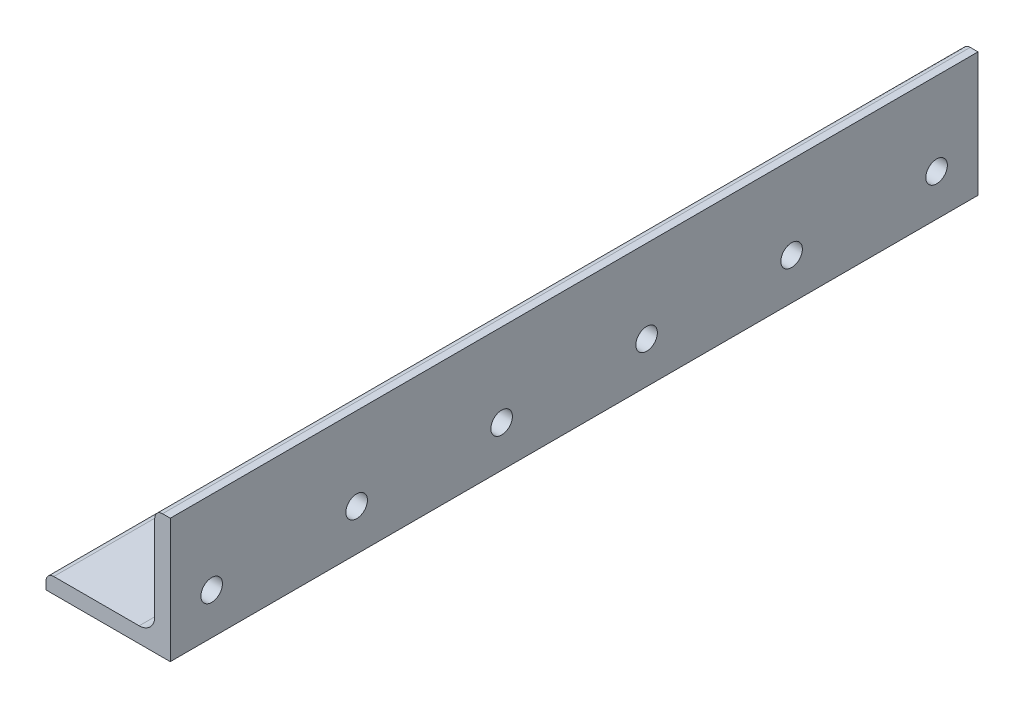
SolidWorks part; units mm, degrees
ref_plane "Front Plane" through (0, 0, 0) normal (0, 0, 1) x (1, 0, 0)
ref_plane "Top Plane" through (0, 0, 0) normal (0, 1, 0) x (1, 0, 0)
ref_plane "Right Plane" through (0, 0, 0) normal (1, 0, 0) x (0, 0, -1)
sketch "Sketch0" plane through (0, 0, 0) normal (0, 0, 1) x (1, 0, 0)
  line L0 (-19.05, -19.05) -> (19.05, -19.05)
  line L1 (19.05, -19.05) -> (19.05, 19.05)
  line L2 (19.05, 0) -> (0, 0) construction
  line L3 (0, 0) -> (0, -19.05) construction
  line L4 (14.2875, -9.5123) -> (14.2875, 19.05) construction
  line L5 (9.5123, -14.2875) -> (-19.05, -14.2875) construction
  arc A0 (14.2875, -9.5123) -> (9.5123, -14.2875) centre (9.5123, -9.5123) cw
  point P3 (12.8889, -12.8889)
  dimension "Inside Corner Radius" = 4.7752
  dimension "Outside Width" = 38.1
  dimension "Wall Thickness" = 4.7625
  dimension "D2" = 4.7625
  dimension "Outside Height" = 38.1
  dimension "Inside Height" = 33.3375
  dimension "Inside Width" = 33.3375
sketch "Sketch1" plane through (0, 0, 0) normal (1, 0, 0) x (0, 0, -1)
  line L0 (152.4, 0) -> (-152.4, 0)
  point P4 (0, 0)
  dimension "Length" = 304.8
sketch "Sketch2" plane through (0, 0, 0) normal (0, 0, 1) x (1, 0, 0)
  line L0 (-19.05, -19.05) -> (19.05, -19.05)
  line L1 (19.05, -19.05) -> (19.05, 19.05)
  line L2 (19.05, 19.05) -> (14.2875, 19.05) construction
  line L3 (14.2875, 16.6688) -> (14.2875, -9.5123)
  line L4 (9.5123, -14.2875) -> (-16.6687, -14.2875)
  line L5 (-19.05, -19.05) -> (-19.05, -14.2875) construction
  line L6 (16.6688, 19.05) -> (19.05, 19.05)
  line L7 (-19.05, -16.6688) -> (-19.05, -19.05)
  line L8 (19.05, 0) -> (0, 0) construction
  line L9 (0, 0) -> (0, -19.05) construction
  arc A0 (14.2875, 16.6688) -> (16.6688, 19.05) centre (16.6688, 16.6688) cw
  arc A1 (-19.05, -16.6688) -> (-16.6687, -14.2875) centre (-16.6687, -16.6688) cw
  arc A2 (14.2875, -9.5123) -> (9.5123, -14.2875) centre (9.5123, -9.5123) cw
  dimension "Inside Radius" = 4.7752
  dimension "Height" = 38.1
  dimension "Width" = 38.1
  dimension "Thickness" = 4.7625
extrude "Boss-Extrude1" add sketch "Sketch2" along normal mid plane 247.65
sketch "Break Locations" plane through (0, 0, 0) normal (1, 0, 0) x (0, 0, -1)
  line L0 (-84.963, 0) -> (84.963, 0)
  line L1 (-123.825, -19.05) -> (-123.825, 19.05) construction
  line L2 (123.825, -19.05) -> (123.825, 19.05) construction
  point P0 (-91.44, 0)
  point P1 (91.44, 0)
  point P10 (0, 0)
  point P11 (84.963, 0)
  point P13 (-84.963, 0)
  dimension "D1" = 32.385
  dimension "D2" = 32.385
  dimension "D3" = 38.862
sketch "Sketch3" plane through (19.05, 0, 0) normal (1, 0, 0) x (0, 0, -1)
  circle A0 centre (111.125, -6.35) radius 3.302 construction
  circle A1 centre (66.675, -6.35) radius 3.302 construction
  circle A2 centre (22.225, -6.35) radius 3.302 construction
  circle A3 centre (-22.225, -6.35) radius 3.302 construction
  circle A4 centre (-66.675, -6.35) radius 3.302 construction
  circle A5 centre (-111.125, -6.35) radius 3.302 construction
  circle A6 centre (111.125, -6.35) radius 3.302
  circle A7 centre (66.675, -6.35) radius 3.302
  circle A8 centre (22.225, -6.35) radius 3.302
  circle A9 centre (-22.225, -6.35) radius 3.302
  circle A10 centre (-66.675, -6.35) radius 3.302
  circle A11 centre (-111.125, -6.35) radius 3.302
extrude "Cut-Extrude1" cut sketch "Sketch3" against normal up to next
sketch "Sketch4" plane through (0, -19.05, 0) normal (0, -1, 0) x (1, 0, 0)
  line L0 (-19.05, -123.825) -> (19.05, -123.825) construction
  line L1 (0, -123.825) -> (0, 123.825) construction
  line L2 (-19.05, 123.825) -> (19.05, 123.825) construction
  circle A0 centre (0, -92.075) radius 3.302
  circle A1 centre (0, -46.355) radius 3.302
  circle A2 centre (0, -0.635) radius 3.302
  circle A3 centre (0, 45.085) radius 3.302
  circle A4 centre (0, 90.805) radius 3.302
  dimension "D1" = 6.604
  dimension "D2" = 31.75
  dimension "D4" = 45.72
  dimension "D3" = 5
extrude "Cut-Extrude2" cut sketch "Sketch4" against normal up to next
equation "\"D1@Break Locations\" = .85 * \"Height@Sketch2\""
equation "\"D2@Break Locations\"=\"D1@Break Locations\""
equation "\"D2@Sketch0\" = \"Wall Thickness@Sketch0\""
equation "\"Thickness@Sketch2\"=\"wall thickness@sketch0\""
equation "\"Height@Sketch2\"=\"outside height@sketch0\""
equation "\"Width@Sketch2\"=\"outside width@sketch0\""
equation "\"Inside Radius@Sketch2\"=\"inside corner radius@sketch0\""
equation "\"D3@Break Locations\"=\"D2@Break Locations\"*1.2"
